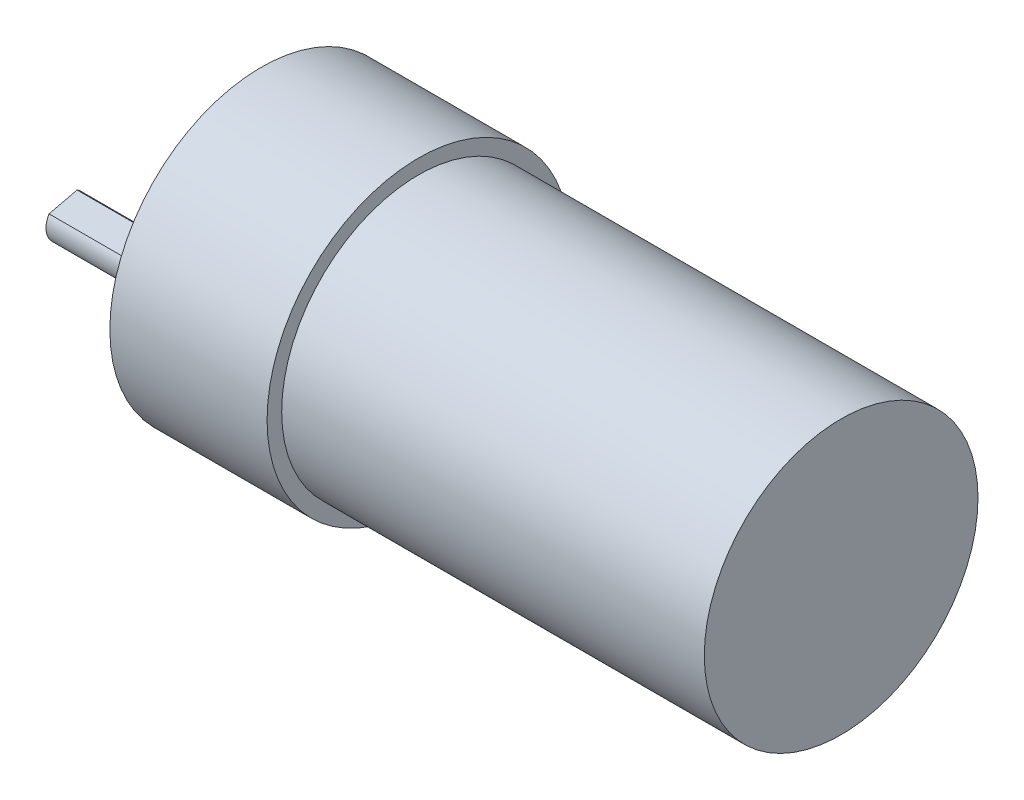
SolidWorks part; units mm, degrees
material "Steel Shell"
ref_plane "Front Plane" through (0, 0, 0) normal (0, 0, 1) x (1, 0, 0)
ref_plane "Top Plane" through (0, 0, 0) normal (0, 1, 0) x (1, 0, 0)
ref_plane "Right Plane" through (0, 0, 0) normal (1, 0, 0) x (0, 0, -1)
sketch "Sketch1" plane through (0, 0, 0) normal (1, 0, 0) x (0, 0, -1)
  circle A0 centre (0, 0) radius 15.875
  dimension "D1" = 31.75
extrude "Extrude1" add sketch "Sketch1" along normal blind 49.022
sketch "Sketch3" plane through (0, 0, 0) normal (-1, 0, 0) x (0, 0, 1)
  circle A0 centre (0, 0) radius 17.5692
extrude "Extrude3" add sketch "Sketch3" along normal blind 18.2372
sketch "Sketch4" plane through (-18.2372, 0, 0) normal (-1, 0, 0) x (0, 0, 1)
  line L0 (0, 0) -> (0, -8.7186) construction
  circle A0 centre (0, -8.7186) radius 2.3749
  dimension "D2" = 4.7498
  dimension "D1" = 8.7186
extrude "Extrude4" add sketch "Sketch4" along normal blind 22.606
sketch "Sketch5" plane through (-18.2372, 0, 0) normal (-1, 0, 0) x (0, 0, 1)
  line L0 (0, 17.5692) -> (0, 13.4556) construction
  circle A0 centre (0, 0) radius 17.5692 construction
  circle A1 centre (0, 13.4556) radius 1.27
  circle A3 centre (0, -8.7186) radius 2.3749 construction
  dimension "D2" = 2.54
  dimension "D1" = 22.1742
extrude "Cut-Extrude1" cut sketch "Sketch5" against normal blind 10
sketch "Sketch6" plane through (-18.2372, 0, 0) normal (-1, 0, 0) x (0, 0, 1)
  line L0 (0, -8.7186) -> (10.2108, -8.7186) construction
  line L1 (0, -8.7186) -> (-10.2108, -8.7186) construction
  circle A0 centre (10.2108, -8.7186) radius 1.27
  circle A4 centre (0, 13.4556) radius 1.27 construction
  circle A5 centre (-10.2108, -8.7186) radius 1.27
  circle A6 centre (0, 13.4556) radius 1.27 construction
  dimension "D1" = 10.2108
extrude "Cut-Extrude2" cut sketch "Sketch6" against normal blind 10
sketch3d "3DSketch3"
  circle A0 centre (-18.2372, -8.7186, 10.2108) radius 1.27 construction
  point P2 (-19.5072, -8.7186, 10.2108)
sketch "Sketch7" plane through (0, -5.9371, -1.4198) normal (0, 0.9726, 0.2326) x (-1, 0, 0)
  line L0 (25.8572, 1.8493) -> (18.2372, 1.8493) construction
  line L1 (25.8572, 6.9456) -> (43.5843, 6.9456)
  line L2 (25.8572, 6.9456) -> (25.8572, -4.0683)
  line L3 (25.8572, -4.0683) -> (43.5843, -4.0683)
  line L4 (43.5843, 6.9456) -> (43.5843, -4.0683)
  line L5 (18.2372, -0.3471) -> (18.2372, 4.4027) construction
  dimension "D1" = 7.62
extrude "Cut-Extrude3" cut sketch "Sketch7" against normal blind 0.6858
sketch "Sketch9" plane through (0, 0, 0) normal (1, 0, 0) x (0, 0, -1)
  line L0 (0, 0) -> (0, 15.875)
  circle A0 centre (0, 0) radius 15.875 construction
ref_plane "Plane3" through (0, 15.875, 0) normal (0, 1, 0) x (-1, 0, 0)
ref_plane "Plane4" through (0, -17.5692, 0) normal (0, -1, 0) x (-1, 0, 0)
ref_plane "Plane5" through (0, -10.5567, -2.5246) normal (0, -0.9726, -0.2326) x (-1, 0, 0)
